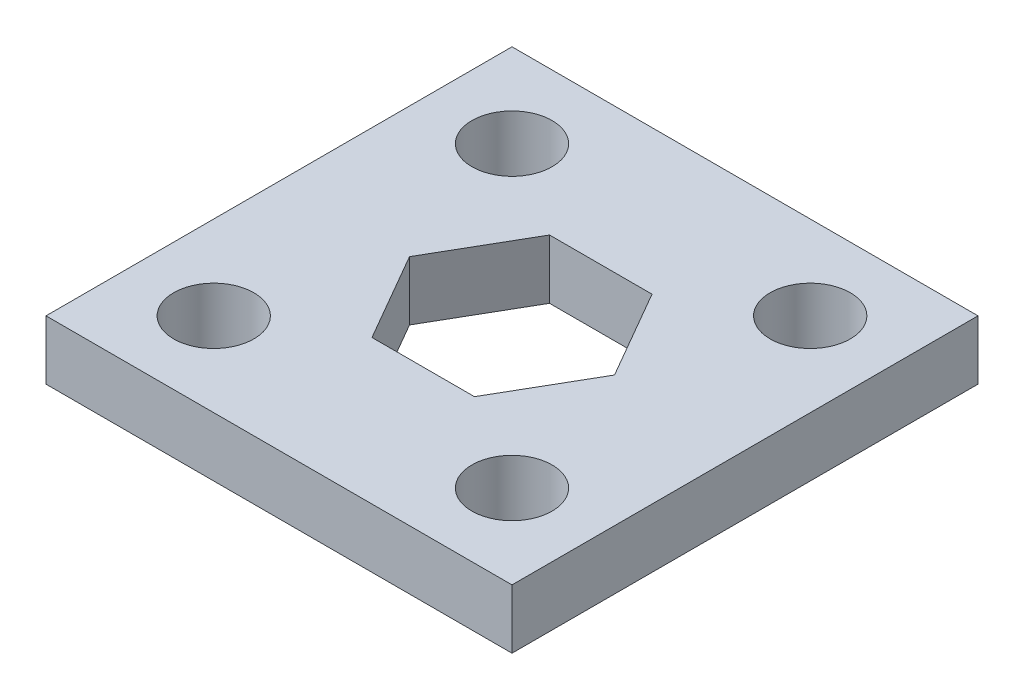
SolidWorks part; units mm, degrees
ref_plane "Front Plane" through (0, 0, 0) normal (0, 0, 1) x (1, 0, 0)
ref_plane "Top Plane" through (0, 0, 0) normal (0, 1, 0) x (1, 0, 0)
ref_plane "Right Plane" through (0, 0, 0) normal (1, 0, 0) x (0, 0, -1)
sketch "Sketch1" plane through (0, 0, 0) normal (0, 1, 0) x (1, 0, 0)
  line L0 (-2.7496, -4.7625) -> (2.7496, -4.7625)
  line L1 (-8, -8) -> (8, -8) construction
  line L2 (-8, -8) -> (-8, 8) construction
  line L3 (-8, 8) -> (8, 8) construction
  line L4 (8, -8) -> (8, 8) construction
  line L5 (-8, -8) -> (8, 8) construction
  line L6 (-8, 8) -> (8, -8) construction
  line L7 (-12.5, -12.5) -> (12.5, -12.5)
  line L8 (-12.5, -12.5) -> (-12.5, 12.5)
  line L9 (-12.5, 12.5) -> (12.5, 12.5)
  line L10 (12.5, -12.5) -> (12.5, 12.5)
  line L11 (-12.5, -12.5) -> (12.5, 12.5) construction
  line L12 (-12.5, 12.5) -> (12.5, -12.5) construction
  line L13 (2.7496, -4.7625) -> (5.4993, 0)
  line L14 (5.4993, 0) -> (2.7496, 4.7625)
  line L15 (2.7496, 4.7625) -> (-2.7496, 4.7625)
  line L16 (-2.7496, 4.7625) -> (-5.4993, 0)
  line L17 (-5.4993, 0) -> (-2.7496, -4.7625)
  circle A0 centre (-8, 8) radius 2.15
  circle A1 centre (8, 8) radius 2.15
  circle A2 centre (8, -8) radius 2.15
  circle A3 centre (-8, -8) radius 2.15
  point P0 (0, 0)
  point P6 (0, 0)
  point P17 (0, 0)
  point P22 (0, 0)
  point P23 (0, 0)
  point P24 (0, 0)
  point P25 (0, 4.7625)
  point P26 (0, 0)
  dimension "D2" = 4.3
  dimension "D1" = 16
  dimension "D3" = 120
  dimension "D4" = 9.525
  dimension "D5" = 25
extrude "Boss-Extrude1" add sketch "Sketch1" along normal mid plane 3.175
